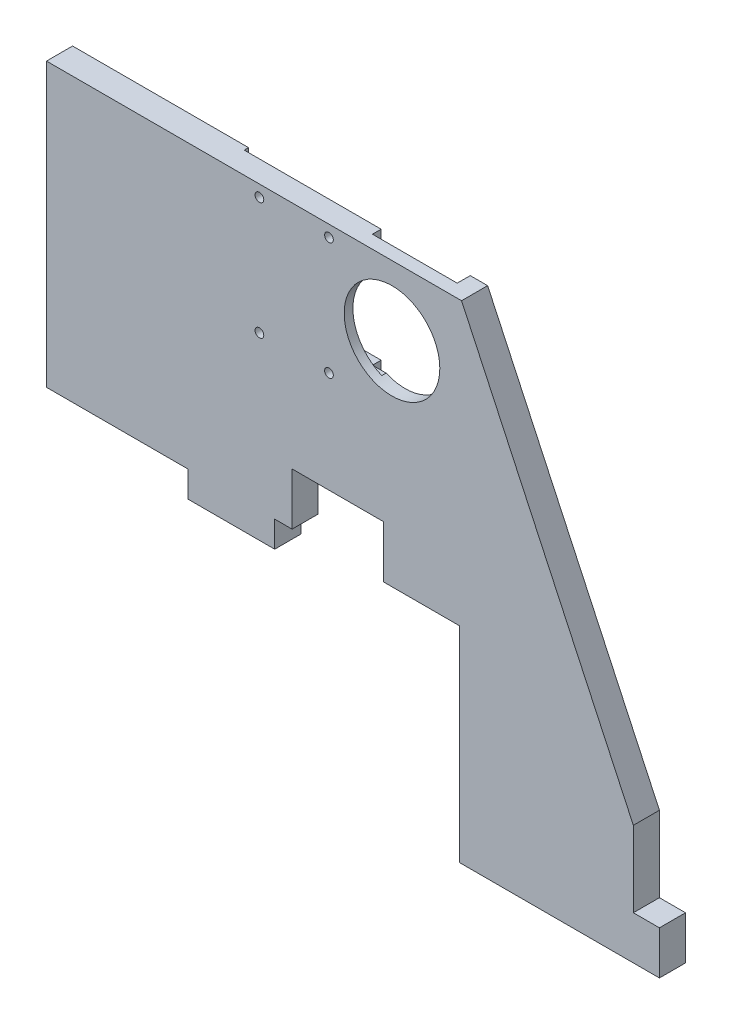
SolidWorks part; units mm, degrees
ref_plane "Plan de face" through (0, 0, 0) normal (0, 0, 1) x (1, 0, 0)
ref_plane "Plan de dessus" through (0, 0, 0) normal (0, 1, 0) x (1, 0, 0)
ref_plane "Plan de droite" through (0, 0, 0) normal (1, 0, 0) x (0, 0, -1)
sketch "Esquisse1" plane through (0, 0, 0) normal (0, 0, 1) x (1, 0, 0)
  line L1 (-67.5, 56.085) -> (67.5, 56.085)
  line L2 (-67.5, 56.085) -> (-67.5, -56.085)
  line L3 (-67.5, -56.085) -> (67.5, -56.085)
  line L4 (67.5, 56.085) -> (67.5, -56.085)
  dimension "D1" = 135
  dimension "D2" = 112.17
  dimension "D3" = 67.5
  dimension "D4" = 56.085
extrude "Boss.-Extru.1" add sketch "Esquisse1" along normal blind 6
sketch "Esquisse2" plane through (0, 0, 6) normal (0, 0, 1) x (1, 0, 0)
  line L0 (-67.5, -56.085) -> (67.5, -56.085) construction
  line L1 (27.5, -56.085) -> (-67.5, -56.085)
  line L2 (27.5, -56.085) -> (27.5, -8.915)
  line L3 (-38.5, -8.915) -> (27.5, -8.915)
  line L4 (-67.5, -56.085) -> (-67.5, -8.915)
  line L5 (-67.5, 56.085) -> (-67.5, -56.085) construction
  line L7 (67.5, -28.665) -> (27.9804, 56.085)
  line L8 (-38.5, -8.915) -> (-67.5, -8.915)
  line L9 (67.5, -56.085) -> (67.5, 56.085) construction
  line L10 (67.5, 56.085) -> (-67.5, 56.085) construction
  line L11 (27.9804, 56.085) -> (67.5, 56.085)
  line L12 (67.5, 56.085) -> (67.5, -28.665)
  dimension "D1" = 47.17
  dimension "D2" = 95
  dimension "D3" = 27.42
  dimension "D4" = 155
  dimension "D5" = 115
extrude "Enlèv. mat.-Extru.1" cut sketch "Esquisse2" against normal blind 6
sketch "Esquisse3" plane through (0, 0, 6) normal (0, 0, 1) x (1, 0, 0)
  line L0 (67.5, -56.085) -> (67.5, -28.665) construction
  line L1 (67.5, -56.085) -> (73.5, -56.085)
  line L2 (67.5, -56.085) -> (67.5, -46.085)
  line L3 (67.5, -46.085) -> (73.5, -46.085)
  line L4 (73.5, -56.085) -> (73.5, -46.085)
  line L6 (-35, -8.915) -> (-15, -8.915)
  line L7 (-35, -8.915) -> (-35, -14.915)
  line L8 (-35, -14.915) -> (-15, -14.915)
  line L9 (-15, -8.915) -> (-15, -14.915)
  line L10 (27.5, -8.915) -> (-67.5, -8.915) construction
  line L16 (27.5, -56.085) -> (27.5, -8.915) construction
  dimension "D3" = 6
  dimension "D4" = 20
  dimension "D5" = 42.5
  dimension "D6" = 10
  dimension "D7" = 6
extrude "Boss.-Extru.2" add sketch "Esquisse3" against normal blind 6
sketch "Esquisse4" plane through (0, 0, 0) normal (0, 0, -1) x (-1, 0, 0)
  line L0 (-27.9804, 56.085) -> (67.5, 56.085) construction
  line L1 (-23.9804, 56.085) -> (27.0196, 56.085)
  line L2 (-23.9804, 56.085) -> (-23.9804, 24.085)
  line L3 (-23.9804, 24.085) -> (27.0196, 24.085)
  line L4 (27.0196, 56.085) -> (27.0196, 24.085)
  dimension "D1" = 4
  dimension "D2" = 51
  dimension "D3" = 32
extrude "Enlèv. mat.-Extru.5" cut sketch "Esquisse4" against normal blind 3
sketch "Esquisse7" plane through (0, 0, 3) normal (0, 0, -1) x (-1, 0, 0)
  line L0 (-23.9804, 56.085) -> (-23.9804, 24.085) construction
  line L1 (27.0196, 56.085) -> (-23.9804, 56.085) construction
  circle A0 centre (-11.9804, 40.085) radius 11
  dimension "D1" = 22
  dimension "D2" = 12
  dimension "D3" = 16
extrude "Enlèv. mat.-Extru.6" cut sketch "Esquisse7" against normal through all
sketch "Esquisse8" plane through (0, 0, 3) normal (0, 0, -1) x (-1, 0, 0)
  line L1 (-9.4804, 50.185) -> (20.5196, 50.185)
  line L2 (-9.4804, 50.185) -> (-9.4804, 29.985)
  line L3 (-9.4804, 29.985) -> (20.5196, 29.985)
  line L4 (20.5196, 50.185) -> (20.5196, 29.985)
  circle A0 centre (-11.9804, 40.085) radius 11 construction
  dimension "D1" = 30
  dimension "D2" = 20.2
  dimension "D3" = 10.1
  dimension "D4" = 32.5
extrude "Enlèv. mat.-Extru.7" cut sketch "Esquisse8" against normal blind 1
sketch "Esquisse9" plane through (0, 0, 3) normal (0, 0, -1) x (-1, 0, 0)
  line L0 (27.0196, 56.085) -> (-23.9804, 56.085) construction
  line L1 (-4.4804, 56.085) -> (20.5196, 56.085)
  line L2 (-4.4804, 56.085) -> (-4.4804, 50.185)
  line L3 (-4.4804, 50.185) -> (20.5196, 50.185)
  line L4 (20.5196, 56.085) -> (20.5196, 50.185)
  dimension "D1" = 25
extrude "Boss.-Extru.4" add sketch "Esquisse9" along normal blind 2
sketch "Esquisse10" plane through (0, 0, 3) normal (0, 0, -1) x (-1, 0, 0)
  line L0 (-23.9804, 24.085) -> (27.0196, 24.085) construction
  line L1 (20.5196, 29.985) -> (-4.4804, 29.985)
  line L2 (20.5196, 29.985) -> (20.5196, 24.085)
  line L3 (20.5196, 24.085) -> (-4.4804, 24.085)
  line L4 (-4.4804, 29.985) -> (-4.4804, 24.085)
  dimension "D1" = 25
extrude "Boss.-Extru.5" add sketch "Esquisse10" along normal blind 2
sketch "Esquisse11" plane through (0, 0, 3) normal (0, 0, -1) x (-1, 0, 0)
  line L1 (20.5196, 56.085) -> (27.0196, 56.085)
  line L2 (20.5196, 56.085) -> (20.5196, 24.085)
  line L3 (20.5196, 24.085) -> (27.0196, 24.085)
  line L4 (27.0196, 56.085) -> (27.0196, 24.085)
extrude "Boss.-Extru.6" add sketch "Esquisse11" along normal blind 2
sketch "Esquisse12" plane through (0, 0, 1) normal (0, 0, -1) x (-1, 0, 0)
  line L0 (27.0196, 24.085) -> (27.0196, 56.085) construction
  line L1 (27.0196, 24.085) -> (27.0196, 56.085) construction
  line L2 (27.0196, 56.085) -> (-4.4804, 56.085) construction
  line L3 (20.5196, 29.985) -> (-4.4804, 29.985) construction
  circle A0 centre (2.5196, 53.435) radius 1
  circle A1 centre (18.5196, 53.435) radius 1
  circle A2 centre (2.5196, 26.435) radius 1
  circle A3 centre (18.5196, 26.435) radius 1
  dimension "D1" = 2
  dimension "D2" = 2
  dimension "D3" = 2
  dimension "D4" = 2
  dimension "D5" = 16
  dimension "D6" = 16
  dimension "D7" = 8.5
  dimension "D8" = 8.5
  dimension "D9" = 2.65
  dimension "D10" = 2.65
  dimension "D11" = 3.55
  dimension "D12" = 3.55
extrude "Enlèv. mat.-Extru.8" cut sketch "Esquisse12" against normal through all
sketch "Esquisse13" plane through (0, 0, 6) normal (0, 0, 1) x (1, 0, 0)
  line L0 (27.5, -8.915) -> (-15, -8.915) construction
  line L1 (-11, -8.915) -> (10, -8.915)
  line L2 (-11, -8.915) -> (-11, 3.085)
  line L3 (-11, 3.085) -> (10, 3.085)
  line L4 (10, -8.915) -> (10, 3.085)
  line L5 (-67.5, 56.085) -> (-67.5, -8.915) construction
  dimension "D1" = 12
  dimension "D2" = 21
  dimension "D3" = 56.5
extrude "Enlèv. mat.-Extru.9" cut sketch "Esquisse13" against normal blind 6 contours L2 L3 L4 L1
equation "\"D3@Esquisse1\"=\"D1@Esquisse1\"/2"
equation "\"D4@Esquisse1\"=\"D2@Esquisse1\"/2"
